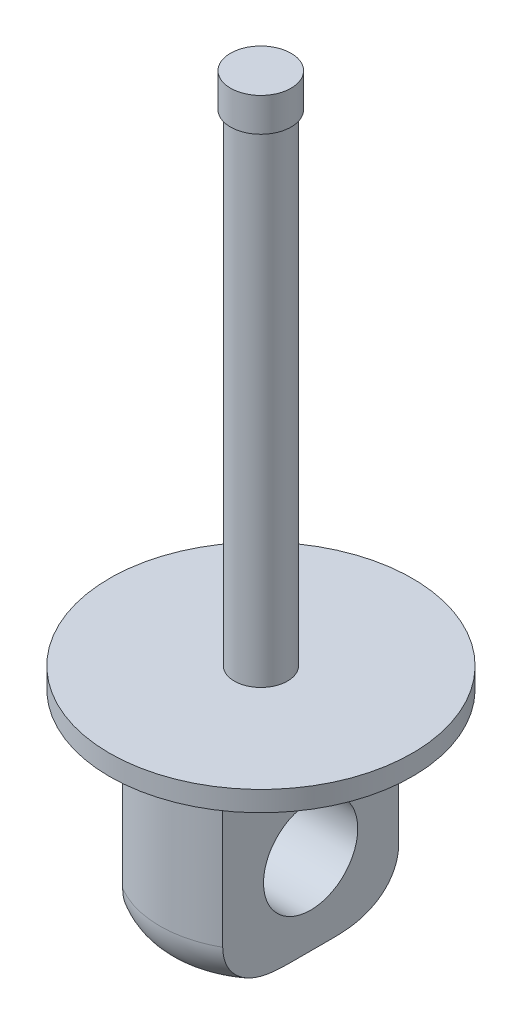
SolidWorks part; units mm, degrees
ref_plane "Front Plane" through (0, 0, 0) normal (0, 0, 1) x (1, 0, 0)
ref_plane "Top Plane" through (0, 0, 0) normal (0, 1, 0) x (1, 0, 0)
ref_plane "Right Plane" through (0, 0, 0) normal (1, 0, 0) x (0, 0, -1)
sketch "Sketch1" plane through (0, 0, 0) normal (0, 1, 0) x (1, 0, 0)
  circle A0 centre (0, 0) radius 2.25
  dimension "D1" = 4.5
extrude "Boss-Extrude1" add sketch "Sketch1" along normal blind 0.3
sketch "Sketch2" plane through (0, 0.3, 0) normal (0, 1, 0) x (1, 0, 0)
  circle A0 centre (0, 0) radius 0.395
  dimension "D1" = 0.79
extrude "Boss-Extrude2" add sketch "Sketch2" along normal blind 7.5
sketch "Sketch13" plane through (0, 0, 0) normal (0, 0, 1) x (1, 0, 0)
  line L1 (-0.0021, 7.4552) -> (-0.4521, 7.4552)
  line L2 (-0.0021, 7.4552) -> (-0.0021, 7.9552)
  line L3 (-0.0021, 7.9552) -> (-0.4521, 7.9552)
  line L4 (-0.4521, 7.4552) -> (-0.4521, 7.9552)
  line L5 (-0.0021, 7.4552) -> (-0.4521, 7.9552) construction
  line L6 (-0.0021, 7.9552) -> (-0.4521, 7.4552) construction
  point P4 (-0.2271, 7.7052)
  dimension "D1" = 0.5
  dimension "D2" = 0.45
sketch "Sketch16" plane through (0, 0, 0) normal (0, 1, 0) x (1, 0, 0)
  circle A0 centre (0, 0) radius 1.5
  dimension "D1" = 3
extrude "Boss-Extrude3" add sketch "Sketch16" against normal blind 3
sketch "Sketch17" plane through (0, 0, 0) normal (0, 0, 1) x (1, 0, 0)
  line L1 (-0.7619, -0.3919) -> (-1.8368, -0.3919)
  line L2 (-0.7619, -0.3919) -> (-0.7619, -3.3729)
  line L3 (-0.7619, -3.3729) -> (-1.8368, -3.3729)
  line L4 (-1.8368, -0.3919) -> (-1.8368, -3.3729)
  line L5 (-0.7619, -0.3919) -> (-1.8368, -3.3729) construction
  line L6 (-0.7619, -3.3729) -> (-1.8368, -0.3919) construction
  line L7 (0.7381, -0.3377) -> (2.2194, -0.3377)
  line L8 (0.7381, -0.3377) -> (0.7381, -3.2659)
  line L9 (0.7381, -3.2659) -> (2.2194, -3.2659)
  line L10 (2.2194, -0.3377) -> (2.2194, -3.2659)
  line L11 (0.7381, -0.3377) -> (2.2194, -3.2659) construction
  line L12 (0.7381, -3.2659) -> (2.2194, -0.3377) construction
  point P4 (-1.2994, -1.8824)
  point P9 (1.4787, -1.8018)
  dimension "D1" = 1.5
extrude "Cut-Extrude1" cut sketch "Sketch17" against normal through all both and the other way through all
sketch "Sketch18" plane through (0, 0, 0) normal (1, 0, 0) x (0, 0, -1)
  circle A0 centre (0, -1.7751) radius 0.7
  dimension "D1" = 1.4
extrude "Cut-Extrude2" cut sketch "Sketch18" against normal through all both and the other way through all
fillet "Fillet4" radius 0.7 2 edges at (-0.0138, -3, 1.4999) (-0.0138, -3, -1.4999)
revolve "Revolve1" add sketch "Sketch13" angle 360 about L2
scale "Scale1" scale about centroid uniform scaling yes scale factor 10
scale "Scale2" scale about centroid uniform scaling yes scale factor 10
scale "Scale3" scale about centroid uniform scaling yes scale factor 0.1
scale "Scale4" scale about centroid uniform scaling yes scale factor 0.1
